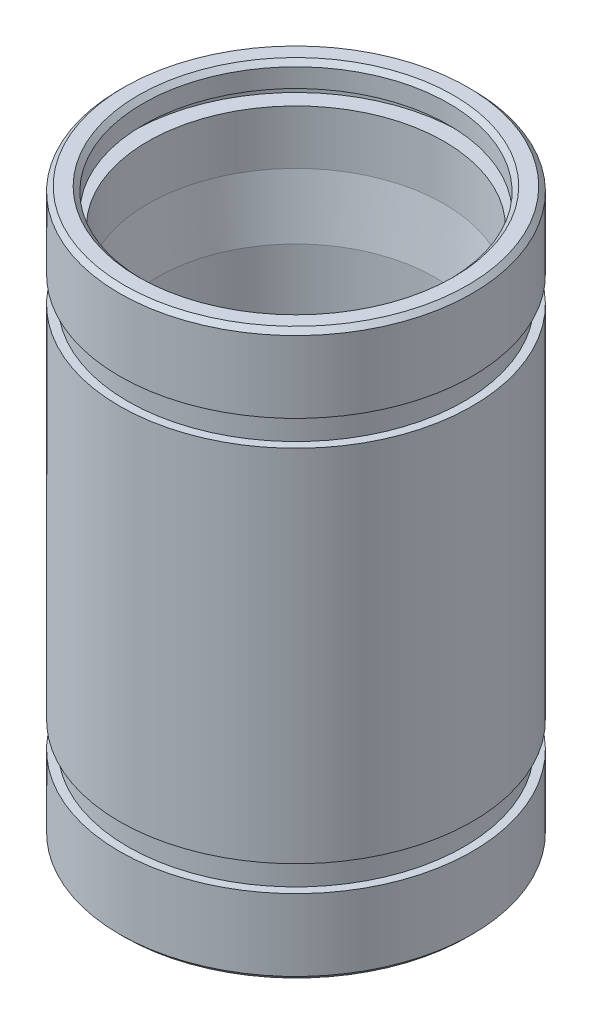
SolidWorks part; units mm, degrees
ref_plane "Front Plane" through (0, 0, 0) normal (0, 0, 1) x (1, 0, 0)
ref_plane "Top Plane" through (0, 0, 0) normal (0, 1, 0) x (1, 0, 0)
ref_plane "Right Plane" through (0, 0, 0) normal (1, 0, 0) x (0, 0, -1)
sketch "Sketch1" plane through (0, 0, 0) normal (1, 0, 0) x (0, 0, -1)
  line L0 (0, 12) -> (0, -12) construction
  line L1 (0, 0) -> (7.5, 0) construction
  line L2 (6.7, 12) -> (7.3, 12)
  line L3 (7.3, 12) -> (7.5, 11.8)
  line L4 (7.5, 11.8) -> (7.5, 8.75)
  line L5 (7.5, 8.75) -> (7.15, 8.75)
  line L6 (7.15, 8.75) -> (7.15, 7.65)
  line L7 (7.15, 7.65) -> (7.5, 7.65)
  line L8 (7.5, 7.65) -> (7.5, -7.65)
  line L9 (6.7, 12) -> (6.5, 11.8)
  line L10 (6.5, 11.8) -> (6.5, 11)
  line L11 (6.5, 11) -> (7, 11)
  line L12 (7, 11) -> (7, 10.5)
  line L13 (7, 10.5) -> (6.3, 10.5)
  line L14 (6.3, 10.5) -> (6.3, 8.2)
  line L15 (6.3, 8.2) -> (5.9, 5.7)
  line L16 (5.9, 5.7) -> (5.9, -5.7)
  line L17 (6.3, -8.2) -> (5.9, -5.7)
  line L18 (6.3, -10.5) -> (6.3, -8.2)
  line L19 (7, -10.5) -> (6.3, -10.5)
  line L20 (7, -11) -> (7, -10.5)
  line L21 (6.5, -11) -> (7, -11)
  line L22 (6.5, -11.8) -> (6.5, -11)
  line L23 (6.7, -12) -> (6.5, -11.8)
  line L24 (7.15, -7.65) -> (7.5, -7.65)
  line L25 (7.15, -8.75) -> (7.15, -7.65)
  line L26 (7.5, -8.75) -> (7.15, -8.75)
  line L27 (7.5, -11.8) -> (7.5, -8.75)
  line L28 (7.3, -12) -> (7.5, -11.8)
  line L29 (6.7, -12) -> (7.3, -12)
  point P0 (0, 0)
  point P28 (5.9, 0)
  dimension "D1" = 0.2
  dimension "D2" = 0.2
  dimension "D3" = 6.5
  dimension "D4" = 7.5
  dimension "D5" = 3.25
  dimension "D6" = 5.9
  dimension "D7" = 7
  dimension "6.3" = 6.3
  dimension "D8" = 0.5
  dimension "D9" = 1.1
  dimension "D10" = 15.3
  dimension "D11" = 7.15
  dimension "D12" = 2.5
  dimension "D13" = 0.8
  dimension "D14" = 11.4
revolve "Revolve1" add sketch "Sketch1" angle 360 about L0
